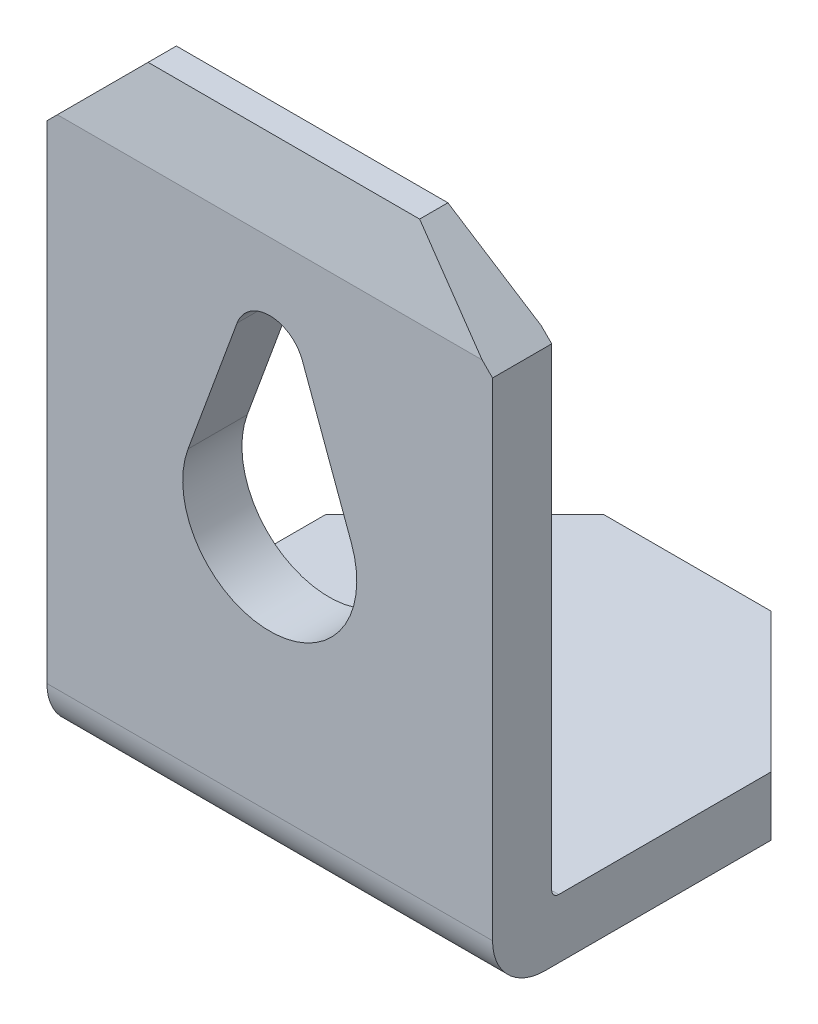
SolidWorks part; units mm, degrees
ref_plane "Front Plane" through (0, 0, 0) normal (0, 0, 1) x (1, 0, 0)
ref_plane "Top Plane" through (0, 0, 0) normal (0, 1, 0) x (1, 0, 0)
ref_plane "Right Plane" through (0, 0, 0) normal (1, 0, 0) x (0, 0, -1)
sketch "Sketch1" plane through (0, 0, 0) normal (1, 0, 0) x (0, 0, -1)
  line L0 (0, 0.1) -> (0, 7.05)
  line L1 (0, 7.05) -> (-0.2414, 8.15)
  line L2 (-0.2414, 8.15) -> (-0.6471, 8.15)
  line L3 (-0.6471, 8.15) -> (-0.85, 7.05)
  line L4 (-0.85, 7.05) -> (-0.85, -0.1)
  line L5 (-0.1, -0.85) -> (5.15, -0.85)
  line L6 (5.15, -0.85) -> (5.15, 0)
  line L7 (5.15, 0) -> (0.1, 0)
  arc A0 (-0.85, -0.1) -> (-0.1, -0.85) centre (-0.1, -0.1) ccw
  arc A1 (0, 0.1) -> (0.1, 0) centre (0.1, 0.1) ccw
  point P3 (5.15, -0.425)
  point P14 (0, 0)
  dimension "D6" = 0.75
  dimension "D7" = 0.1
  dimension "D1" = 9
  dimension "D2" = 0.85
  dimension "D3" = 1.1
  dimension "D5" = 0.85
  dimension "D4" = 6
  dimension "D8" = 0.2414
  dimension "D9" = 0.6471
extrude "Boss-Extrude1" add sketch "Sketch1" along normal blind 6.4
chamfer "Chamfer3" distance 2 angle 45 2 edges at (6.4, -0.425, -5.15) (0, -0.425, -5.15)
sketch "Sketch4" plane through (0, 0, 0.85) normal (0, 0, 1) x (1, 0, 0)
  line L0 (0, 6.9) -> (1.25, 8.15)
  line L1 (0, 7.05) -> (0, -0.1) construction
  line L2 (6.4, 8.15) -> (0, 8.15) construction
  line L4 (5.15, 8.15) -> (6.4, 6.9)
  line L5 (6.4, 7.05) -> (6.4, -0.1) construction
  line L6 (0, 6.9) -> (0, 8.15)
  line L7 (0, 8.15) -> (1.25, 8.15)
  line L8 (5.15, 8.15) -> (6.4, 8.15)
  line L9 (6.4, 8.15) -> (6.4, 6.9)
  dimension "D1" = 1.25
  dimension "D2" = 1.25
  dimension "D3" = 1.25
extrude "Cut-Extrude1" cut sketch "Sketch4" against normal up to surface (0.85 mm away) up to face at (3.2, 3.575, 0)
sketch "Sketch5" plane through (0, 0, 0.85) normal (0, 0, 1) x (1, 0, 0)
  line L0 (5.15, 8.15) -> (1.25, 8.15) construction
  line L1 (2.7306, 5.7488) -> (2.0266, 3.8307)
  line L2 (3.6696, 5.7481) -> (4.3734, 3.8307)
  line L3 (0, 6.9) -> (0, -0.1) construction
  arc A0 (2.0266, 3.8307) -> (4.3734, 3.8307) centre (3.2, 3.4) ccw
  arc A1 (3.6696, 5.7481) -> (2.7306, 5.7488) centre (3.2, 5.5765) ccw
  dimension "D1" = 2.5
  dimension "D3" = 1
  dimension "D2" = 4.75
  dimension "D4" = 2.1765
  dimension "D5" = 2.0266
  dimension "D6" = 2.7306
  dimension "D7" = 3.6696
extrude "Cut-Extrude2" cut sketch "Sketch5" against normal up to surface (0.85 mm away) up to face at (3.2, 4.6833, 0)
sketch "Sketch6" plane through (0, 0, 0) normal (0, 1, 0) x (1, 0, 0)
  line L0 (6.4, 3.15) -> (6.4, 0.1) construction
  line L1 (6.4, 3.15) -> (4.4, 5.15) construction
  line L2 (4.4, 5.15) -> (2, 5.15) construction
  line L3 (2, 5.15) -> (0, 3.15) construction
  line L4 (0, 3.15) -> (0, 0.1) construction
  line L5 (6.4, 3.15) -> (6.4, 0.1)
  line L6 (6.4, 3.15) -> (4.4, 5.15)
  line L7 (4.4, 5.15) -> (2, 5.15)
  line L8 (2, 5.15) -> (0, 3.15)
  line L9 (0, 3.15) -> (0, 0.1)
equation "\"D5@Sketch1\"=\"D2@Sketch1\""
